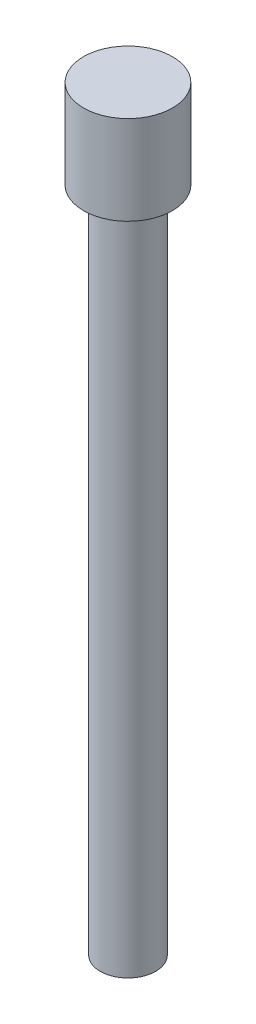
SolidWorks part; units mm, degrees
ref_plane "Front Plane" through (0, 0, 0) normal (0, 0, 1) x (1, 0, 0)
ref_plane "Top Plane" through (0, 0, 0) normal (0, 1, 0) x (1, 0, 0)
ref_plane "Right Plane" through (0, 0, 0) normal (1, 0, 0) x (0, 0, -1)
sketch "Sketch1" plane through (0, 0, 0) normal (0, 1, 0) x (1, 0, 0)
  circle A0 centre (0, 0) radius 1.25
  dimension "D1" = 2.5
extrude "Boss-Extrude1" add sketch "Sketch1" along normal blind 30
sketch "Sketch2" plane through (0, 30, 0) normal (0, 1, 0) x (1, 0, 0)
  circle A0 centre (0, 0) radius 2
  dimension "D1" = 4
extrude "Boss-Extrude2" add sketch "Sketch2" along normal blind 4
